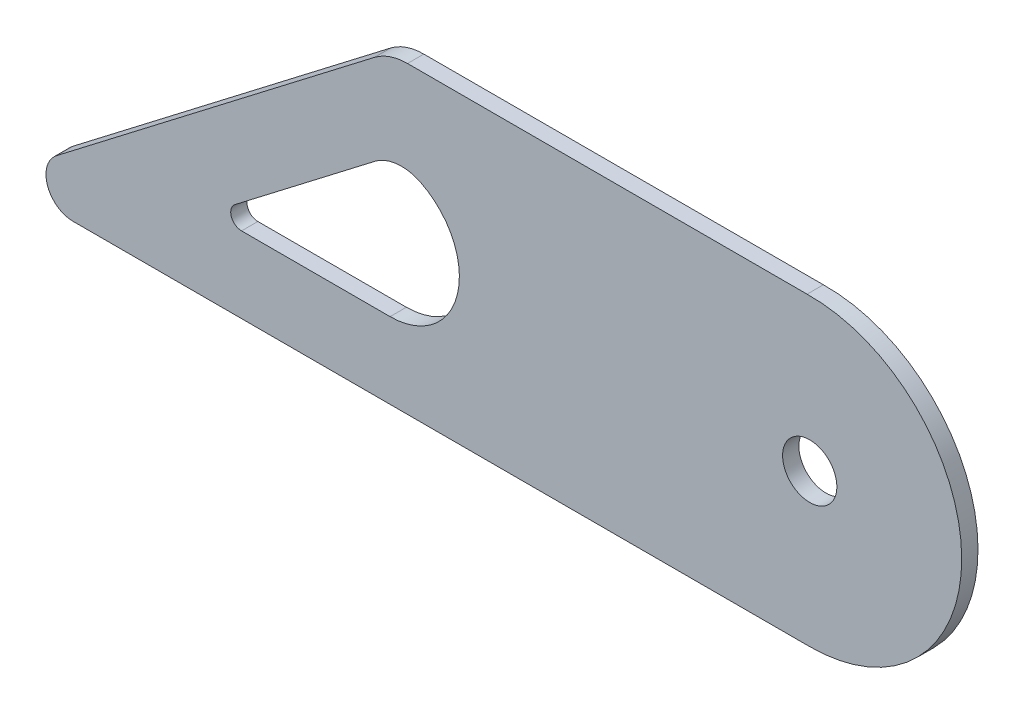
SolidWorks part; units mm, degrees
ref_plane "Front" through (0, 0, 0) normal (0, 0, 1) x (1, 0, 0)
ref_plane "Top" through (0, 0, 0) normal (0, 1, 0) x (1, 0, 0)
ref_plane "Right" through (0, 0, 0) normal (1, 0, 0) x (0, 0, -1)
sketch "Sketch2" plane through (0, 0, 0) normal (0, 0, 1) x (1, 0, 0)
  line L0 (-398.4685, -10.3406) -> (-691.2809, -235.1491)
  line L7 (-526.9809, -192.047) -> (-398.0142, -93.0319)
  line L9 (-384.0981, -209.9789) -> (-520.8912, -209.9789)
  line L10 (2.433, -279.9789) -> (-676.0565, -279.9789)
  line L11 (-368.0198, 0) -> (0, 0)
  arc A0 (2.433, -279.9789) -> (0, 0) centre (2.433, -139.9789) ccw
  arc A4 (-368.0198, 0) -> (-398.4685, -10.3406) centre (-368.0198, -50) ccw
  arc A6 (-356.1154, -88.8101) -> (-384.0981, -209.9789) centre (-384.0981, -146.1633) cw
  arc A7 (-398.0142, -93.0319) -> (-356.1154, -88.8101) centre (-373.6552, -124.7595) cw
  arc A8 (-526.9809, -192.047) -> (-520.8912, -209.9789) centre (-520.8912, -199.9789) ccw
  circle A9 centre (2.433, -139.9789) radius 25
  arc A10 (-691.2809, -235.1491) -> (-676.0565, -279.9789) centre (-676.0565, -254.9789) ccw
  point P0 (2.433, -139.9789)
  point P14 (-384.0981, -2.6557)
  dimension "D3" = 140
  dimension "D4" = 25
  dimension "D7" = 40
  dimension "D8" = 10.443
  dimension "D9" = 10
  dimension "D10" = 386.5311
  dimension "D11" = 63.8155
  dimension "D12" = 50
  dimension "D2" = 678.4895
  dimension "D5" = 70
  dimension "D6" = 65.8666
  dimension "D13" = 369.1585
extrude "Boss-Extrude1" add sketch "Sketch2" along normal mid plane 15
